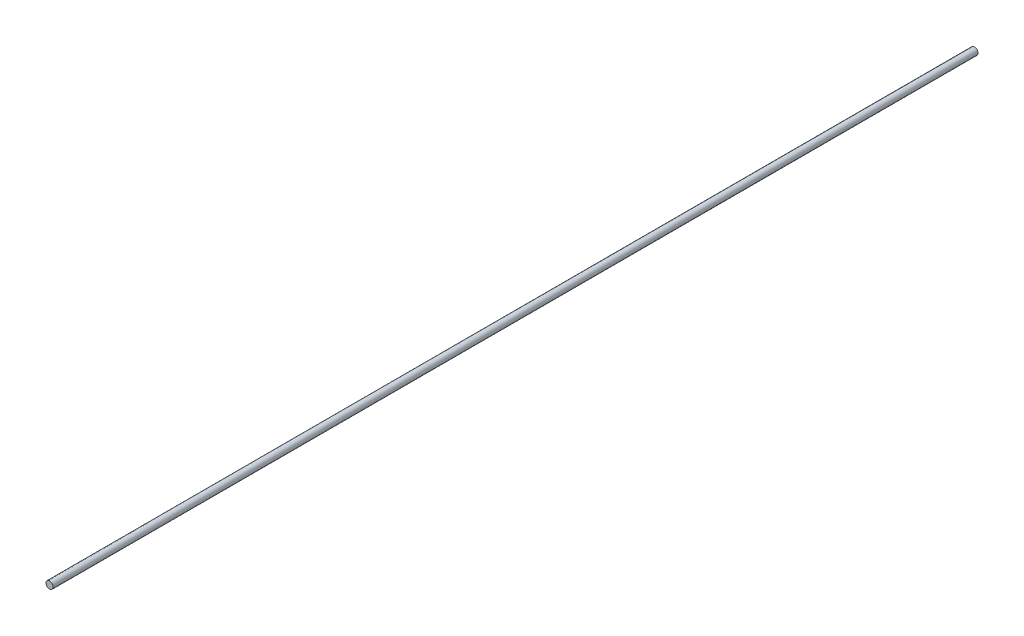
SolidWorks part; units mm, degrees
material "Plain Carbon Steel"
ref_plane "Front Plane" through (0, 0, 0) normal (0, 0, 1) x (1, 0, 0)
ref_plane "Top Plane" through (0, 0, 0) normal (0, 1, 0) x (1, 0, 0)
ref_plane "Right Plane" through (0, 0, 0) normal (1, 0, 0) x (0, 0, -1)
sketch "Sketch1" plane through (0, 0, 0) normal (0, 0, 1) x (1, 0, 0)
  circle A0 centre (0, 0) radius 4
  dimension "D1" = 8
extrude "Boss-Extrude1" add sketch "Sketch1" along normal blind 1040
